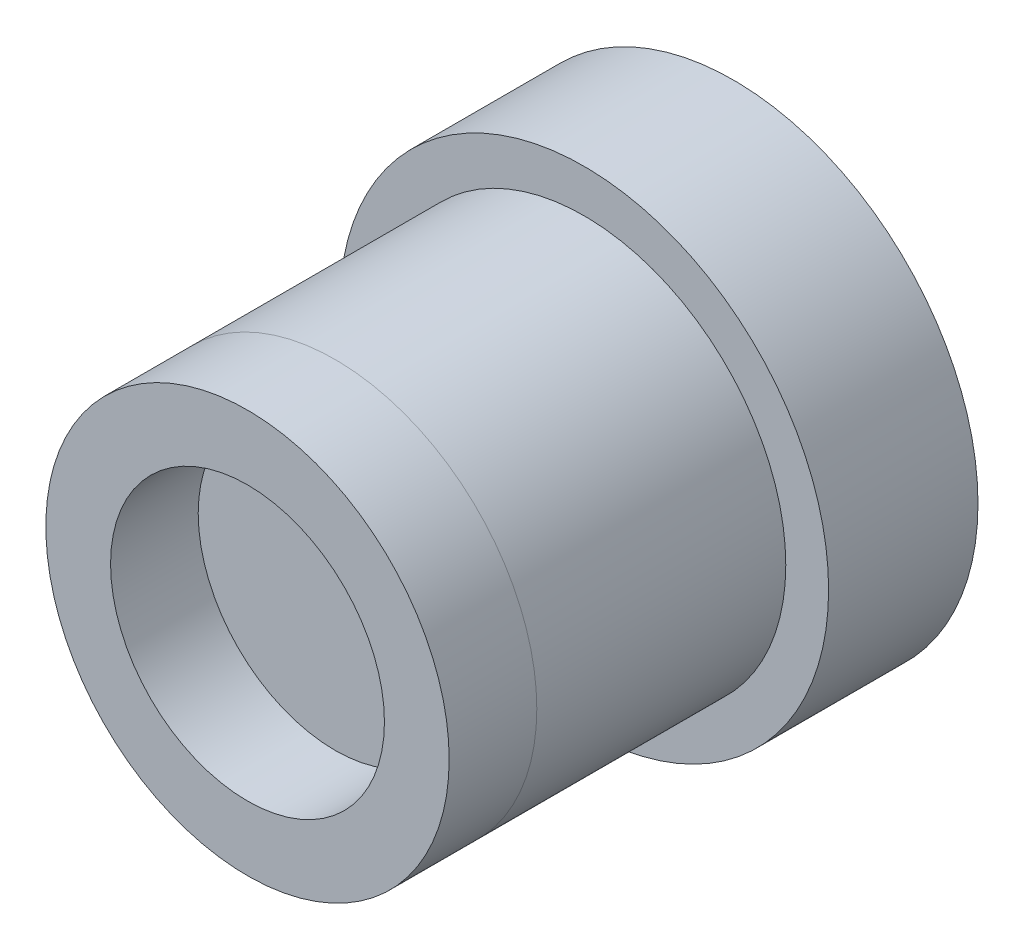
SolidWorks part; units mm, degrees
ref_plane "Front Plane" through (0, 0, 0) normal (0, 0, 1) x (1, 0, 0)
ref_plane "Top Plane" through (0, 0, 0) normal (0, 1, 0) x (1, 0, 0)
ref_plane "Right Plane" through (0, 0, 0) normal (1, 0, 0) x (0, 0, -1)
sketch "Sketch1" plane through (0, 0, 0) normal (0, 0, 1) x (1, 0, 0)
  circle A1 centre (0, 0) radius 4.91
  dimension "D1" = 9.82
extrude "Boss-Extrude1" add sketch "Sketch1" along normal blind 8 contours A1
sketch "Sketch2" plane through (0, 0, 8) normal (0, 0, 1) x (1, 0, 0)
  circle A0 centre (0, 0) radius 2.75
  circle A1 centre (0, 0) radius 4.05
  dimension "D1" = 8.1
  dimension "D2" = 5.5
extrude "Boss-Extrude2" add sketch "Sketch2" along normal blind 1.76 separate body
sketch "Sketch3" plane through (0, 0, 8) normal (0, 0, 1) x (1, 0, 0)
  circle A0 centre (0, 0) radius 4.91
  circle A1 centre (0, 0) radius 4.05
  dimension "D1" = 9.82
  dimension "D2" = 8.1
extrude "Cut-Extrude1" cut sketch "Sketch3" against normal blind 5
